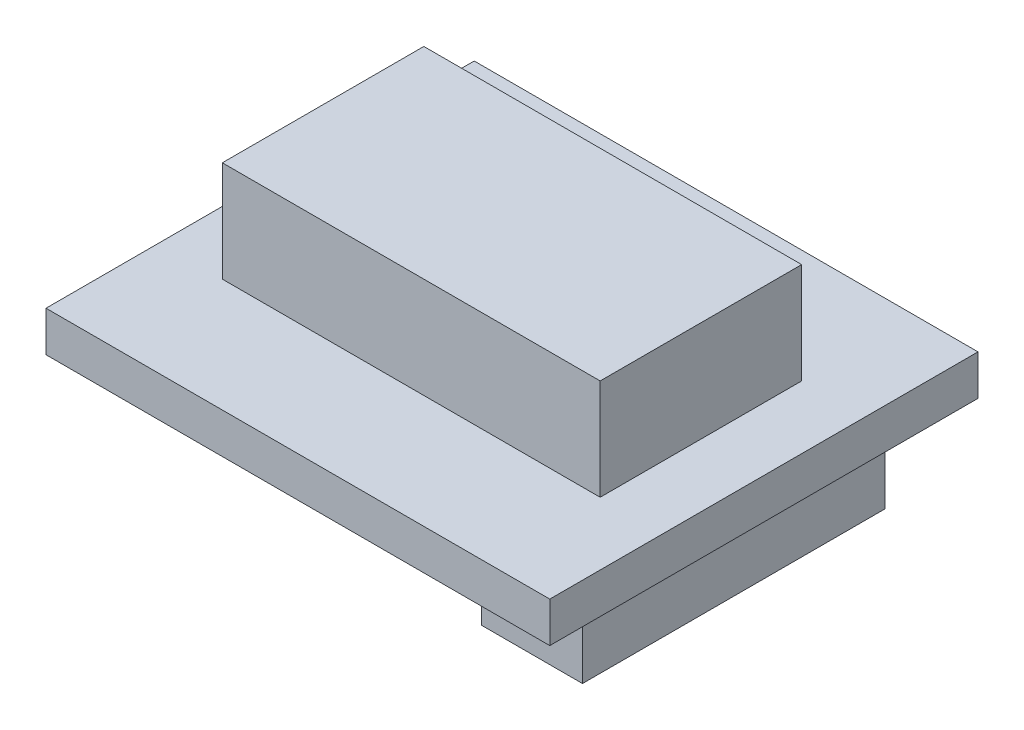
SolidWorks part; units mm, degrees
ref_plane "前视基准面" through (0, 0, 0) normal (0, 0, 1) x (1, 0, 0)
ref_plane "上视基准面" through (0, 0, 0) normal (0, 1, 0) x (1, 0, 0)
ref_plane "右视基准面" through (0, 0, 0) normal (1, 0, 0) x (0, 0, -1)
sketch "草图1" plane through (0, 0, 0) normal (0, 1, 0) x (1, 0, 0)
  line L1 (-50, 42.5) -> (50, 42.5)
  line L2 (-50, 42.5) -> (-50, -42.5)
  line L3 (-50, -42.5) -> (50, -42.5)
  line L4 (50, 42.5) -> (50, -42.5)
  line L5 (-50, 42.5) -> (50, -42.5) construction
  line L6 (-50, -42.5) -> (50, 42.5) construction
  point P0 (0, 0)
  dimension "D1" = 100
  dimension "D2" = 85
extrude "凸台-拉伸1" add sketch "草图1" along normal blind 8
sketch "草图2" plane through (0, 8, 0) normal (0, 1, 0) x (1, 0, 0)
  line L1 (-37.5, 20) -> (37.5, 20)
  line L2 (-37.5, 20) -> (-37.5, -20)
  line L3 (-37.5, -20) -> (37.5, -20)
  line L4 (37.5, 20) -> (37.5, -20)
  line L5 (-37.5, 20) -> (37.5, -20) construction
  line L6 (-37.5, -20) -> (37.5, 20) construction
  point P0 (0, 0)
  dimension "D1" = 75
  dimension "D2" = 40
extrude "凸台-拉伸2" add sketch "草图2" along normal blind 20
sketch "草图3" plane through (0, 0, 0) normal (0, -1, 0) x (1, 0, 0)
  line L1 (24.7687, 30.7771) -> (44.7687, 30.7771)
  line L2 (24.7687, 30.7771) -> (24.7687, -29.2229)
  line L3 (24.7687, -29.2229) -> (44.7687, -29.2229)
  line L4 (44.7687, 30.7771) -> (44.7687, -29.2229)
  line L5 (24.7687, 30.7771) -> (44.7687, -29.2229) construction
  line L6 (24.7687, -29.2229) -> (44.7687, 30.7771) construction
  point P0 (34.7687, 0.7771)
  dimension "D1" = 20
  dimension "D2" = 60
extrude "凸台-拉伸3" add sketch "草图3" along normal blind 15
sketch "草图4" plane through (0, 0, 0) normal (0, -1, 0) x (1, 0, 0)
  line L0 (-35, 12.5) -> (15, 12.5) construction
  line L1 (15, 12.5) -> (15, -12.5) construction
  line L2 (15, -12.5) -> (-35, -12.5) construction
  line L3 (-35, -12.5) -> (-35, 12.5) construction
  line L4 (-50, -42.5) -> (-50, 42.5) construction
  circle A0 centre (15, -12.5) radius 1.6
  circle A1 centre (15, 12.5) radius 1.6
  circle A2 centre (-35, 12.5) radius 1.6
  circle A3 centre (-35, -12.5) radius 1.6
  dimension "D1" = 3.2
  dimension "D2" = 3.2
  dimension "D3" = 3.2
  dimension "D4" = 3.2
  dimension "D5" = 25
  dimension "D6" = 50
  dimension "D7" = 12.5
  dimension "D8" = 15
extrude "切除-拉伸1" cut sketch "草图4" against normal blind 8
